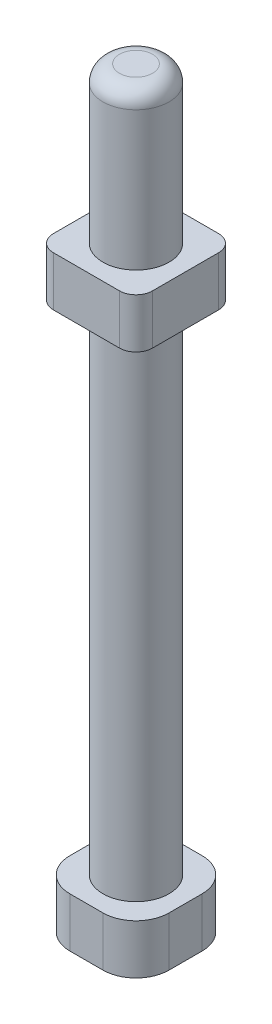
SolidWorks part; units mm, degrees
ref_plane "Front Plane" through (0, 0, 0) normal (0, 0, 1) x (1, 0, 0)
ref_plane "Top Plane" through (0, 0, 0) normal (0, 1, 0) x (1, 0, 0)
ref_plane "Right Plane" through (0, 0, 0) normal (1, 0, 0) x (0, 0, -1)
sketch "Sketch2" plane through (0, 0, 0) normal (0, 1, 0) x (1, 0, 0)
  line L1 (-3, 3) -> (3, 3)
  line L2 (-3, 3) -> (-3, -3)
  line L3 (-3, -3) -> (3, -3)
  line L4 (3, 3) -> (3, -3)
  line L5 (-3, 3) -> (3, -3) construction
  line L6 (-3, -3) -> (3, 3) construction
  point P0 (0, 0)
  dimension "D1" = 6
  dimension "D2" = 6
extrude "Boss-Extrude1" add sketch "Sketch2" along normal blind 3
fillet "Fillet7" radius 2 4 edges at (-3, 1.5, -3) (3, 1.5, -3) (3, 1.5, 3) (-3, 1.5, 3)
sketch "Sketch3" plane through (0, 3, 0) normal (0, 1, 0) x (1, 0, 0)
  circle A0 centre (0, 0) radius 2
extrude "Boss-Extrude2" add sketch "Sketch3" along normal blind 42.5
fillet "Fillet9" radius 1 1 edges at (0, 45.5, 2)
sketch "Sketch4" plane through (0, 45.5, 0) normal (0, 1, 0) x (1, 0, 0)
  line L1 (3, 3) -> (-3, 3)
  line L2 (3, 3) -> (3, -3)
  line L3 (3, -3) -> (-3, -3)
  line L4 (-3, 3) -> (-3, -3)
  line L5 (3, 3) -> (-3, -3) construction
  line L6 (3, -3) -> (-3, 3) construction
  point P0 (0, 0)
  dimension "D1" = 6
  dimension "D2" = 6
extrude "Boss-Extrude3" add sketch "Sketch4" against normal blind 3 from offset 9.4 offset against normal yes
fillet "Fillet10" radius 1 4 edges at (3, 34.6, -3) (3, 34.6, 3) (-3, 34.6, 3) (-3, 34.6, -3)
